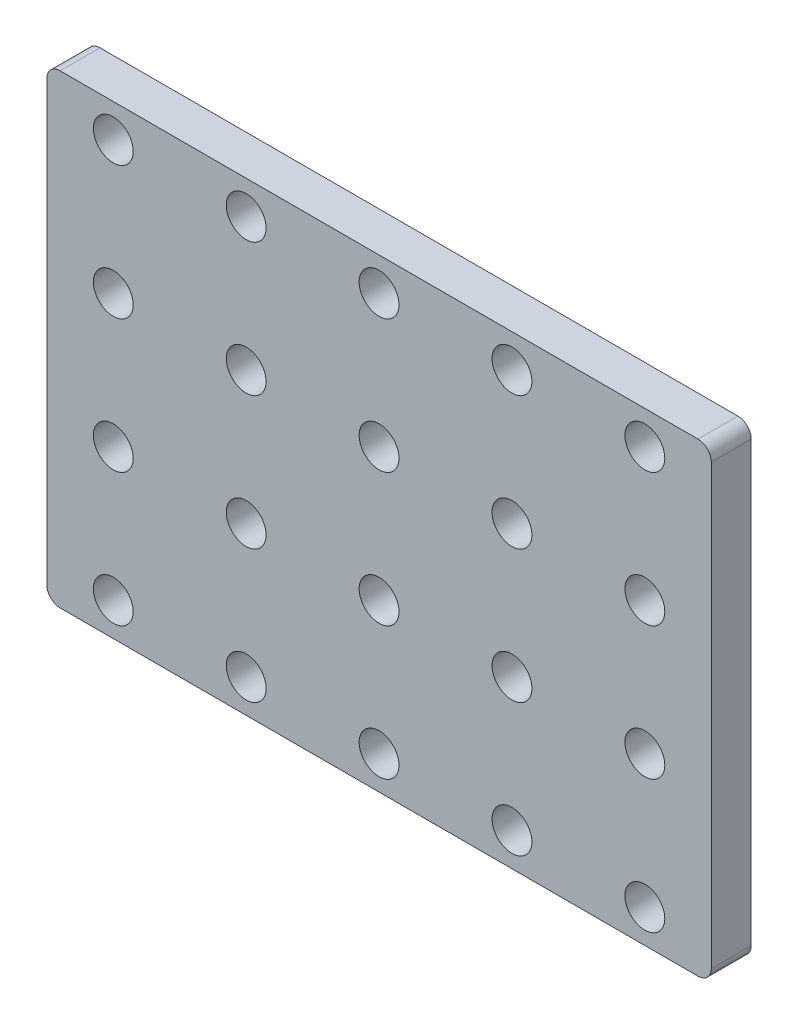
SolidWorks part; units mm, degrees
ref_plane "Plan de face" through (0, 0, 0) normal (0, 0, 1) x (1, 0, 0)
ref_plane "Plan de dessus" through (0, 0, 0) normal (0, 1, 0) x (1, 0, 0)
ref_plane "Plan de droite" through (0, 0, 0) normal (1, 0, 0) x (0, 0, -1)
sketch "Esquisse1" plane through (0, 0, 0) normal (0, 0, 1) x (1, 0, 0)
  line L1 (0, 0) -> (50, 0)
  line L2 (0, 0) -> (0, 35)
  line L3 (0, 35) -> (50, 35)
  line L4 (50, 0) -> (50, 35)
  dimension "D1" = 50
  dimension "D2" = 35
extrude "Boss.-Extru.1" add sketch "Esquisse1" along normal blind 3
sketch "Esquisse2" plane through (0, 0, 3) normal (0, 0, 1) x (1, 0, 0)
  line L0 (50, 35) -> (0, 35) construction
  line L1 (0, 35) -> (0, 0) construction
  line L2 (50, 0) -> (50, 35) construction
  line L3 (0, 0) -> (50, 0) construction
  circle A0 centre (5, 32.5) radius 1.5
  circle A1 centre (15, 32.5) radius 1.5
  circle A2 centre (25, 32.5) radius 1.5
  circle A3 centre (35, 32.5) radius 1.5
  circle A4 centre (45, 32.5) radius 1.5
  circle A5 centre (15, 22.5) radius 1.5
  circle A6 centre (25, 22.5) radius 1.5
  circle A7 centre (35, 22.5) radius 1.5
  circle A8 centre (45, 22.5) radius 1.5
  circle A9 centre (15, 12.5) radius 1.5
  circle A10 centre (25, 12.5) radius 1.5
  circle A11 centre (35, 12.5) radius 1.5
  circle A12 centre (45, 12.5) radius 1.5
  circle A13 centre (15, 2.5) radius 1.5
  circle A14 centre (25, 2.5) radius 1.5
  circle A15 centre (35, 2.5) radius 1.5
  circle A16 centre (45, 2.5) radius 1.5
  circle A17 centre (5, 22.5) radius 1.5
  circle A18 centre (5, 12.5) radius 1.5
  circle A19 centre (5, 2.5) radius 1.5
  dimension "D1" = 3
  dimension "D2" = 2.5
  dimension "D3" = 5
  dimension "D6" = 5
  dimension "D7" = 2.5
  dimension "D4" = 5
  dimension "D5" = 4
extrude "Enlèv. mat.-Extru.1" cut sketch "Esquisse2" against normal blind 3
fillet "Congé1" radius 1 4 edges at (0, 0, 1.5) (50, 0, 1.5) (50, 35, 1.5) (0, 35, 1.5)
